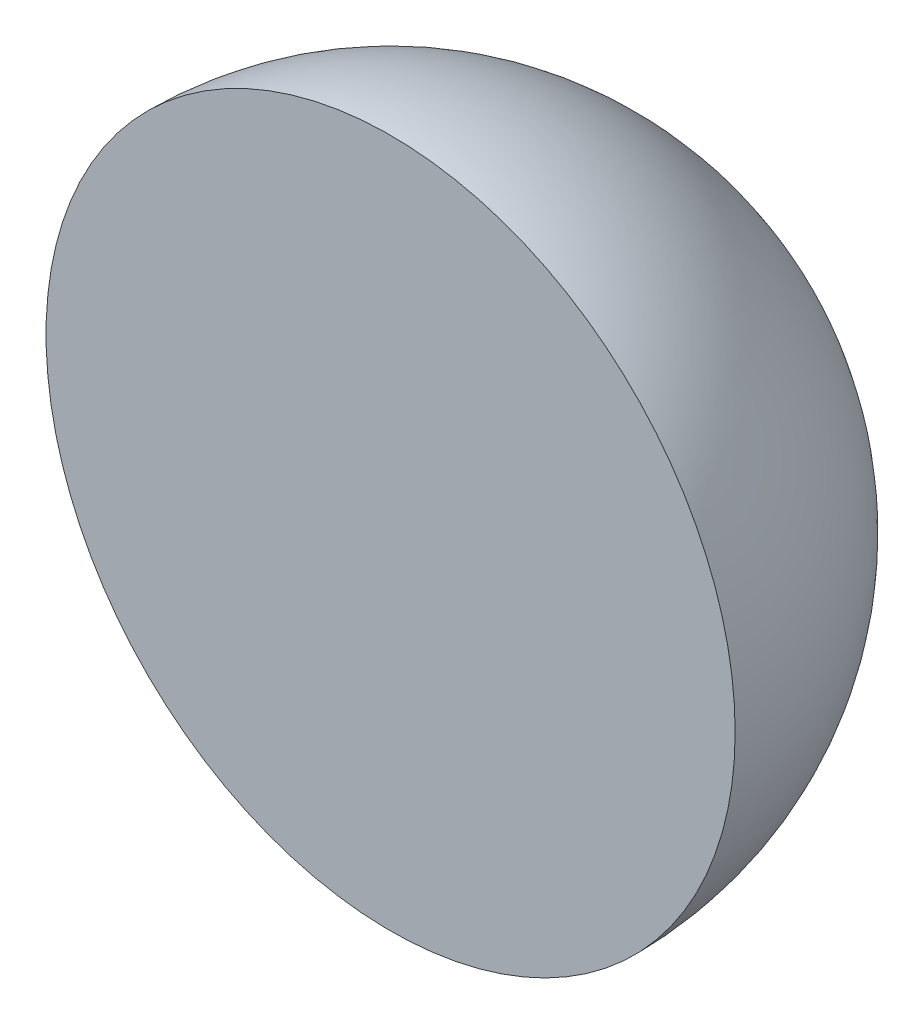
SolidWorks part; units mm, degrees
ref_plane "Front Plane" through (0, 0, 0) normal (0, 0, 1) x (1, 0, 0)
ref_plane "Top Plane" through (0, 0, 0) normal (0, 1, 0) x (1, 0, 0)
ref_plane "Right Plane" through (0, 0, 0) normal (1, 0, 0) x (0, 0, -1)
sketch "Sketch1" plane through (0, 0, 0) normal (0, 1, 0) x (1, 0, 0)
  line L0 (0, 0) -> (0, 31.5)
  line L1 (0, 31.5) -> (0, 0)
  line L2 (0, 0) -> (31.5, 0)
  arc A0 (31.5, 0) -> (0, 31.5) centre (0, 0) ccw
  dimension "D1" = 31.5
revolve "Revolve1" add sketch "Sketch1" angle 360 about L0
equation "\"D1@Sketch1\"=73/2-5"
